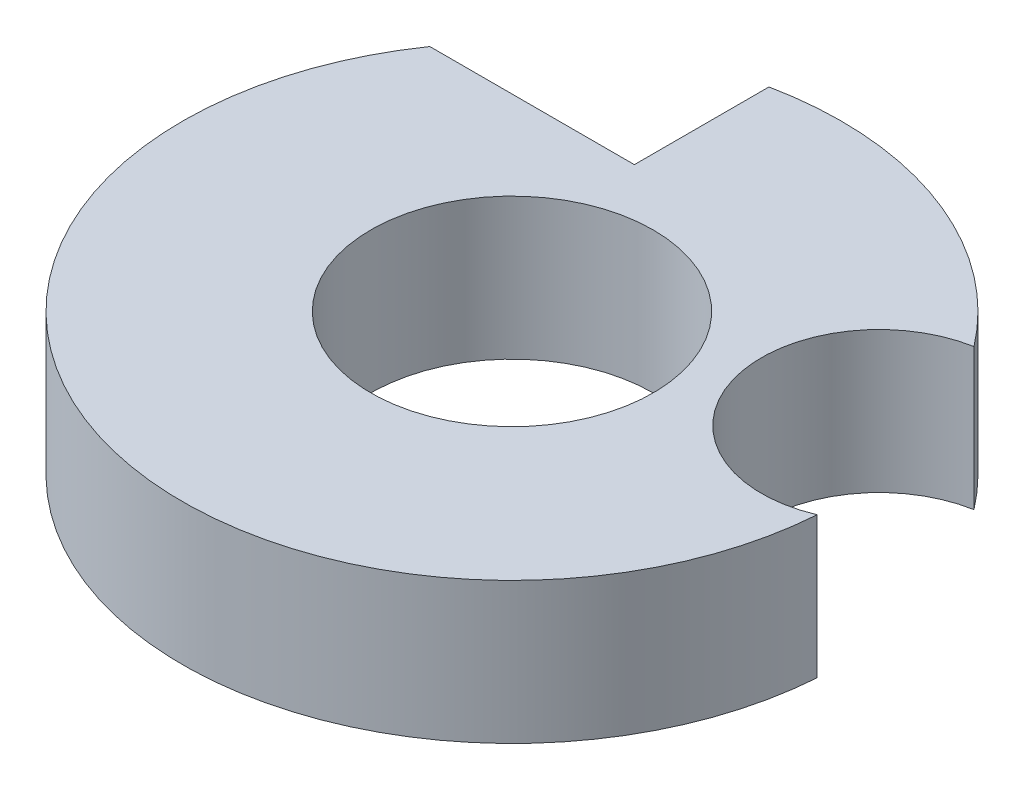
SolidWorks part; units mm, degrees
material "2014-T6"
ref_plane "Спереди" through (0, 0, 0) normal (0, 0, 1) x (1, 0, 0)
ref_plane "Сверху" through (0, 0, 0) normal (0, 1, 0) x (1, 0, 0)
ref_plane "Справа" through (0, 0, 0) normal (1, 0, 0) x (0, 0, -1)
sketch "Эскиз1" plane through (0, 0, 0) normal (0, 0, 1) x (1, 0, 0)
  line L0 (0, 0) -> (0, 25.7486) construction
  line L2 (1.5, 0) -> (3.5, 0)
  line L3 (1.5, 0) -> (1.5, 1.5)
  line L4 (1.5, 1.5) -> (3.5, 1.5)
  line L5 (3.5, 0) -> (3.5, 1.5)
  dimension "D1" = 3
  dimension "D2" = 7
  dimension "D3" = 1.5
revolve "Повернуть1" add sketch "Эскиз1" angle 360 about L0
sketch "Эскиз2" plane through (0, 1.5, 0) normal (0, 1, 0) x (1, 0, 0)
  line L0 (-0.7, 3.4293) -> (-0.7, 2)
  line L1 (-0.7, 2) -> (-2.8723, 2)
  circle A0 centre (0, 0) radius 3.5 construction
  circle A1 centre (0, 0) radius 1.5 construction
  circle A2 centre (3, 0.9) radius 1.25
  circle M2 centre (0, 0) radius 3.5
  dimension "D2" = 2
  dimension "D3" = 2.5
  dimension "D4" = 3
  dimension "D5" = 0.9
  dimension "D1" = 0.7
extrude "Вырез-Вытянуть1" cut sketch "Эскиз2" against normal through all contours L1 L0 M2 | A2 M2
